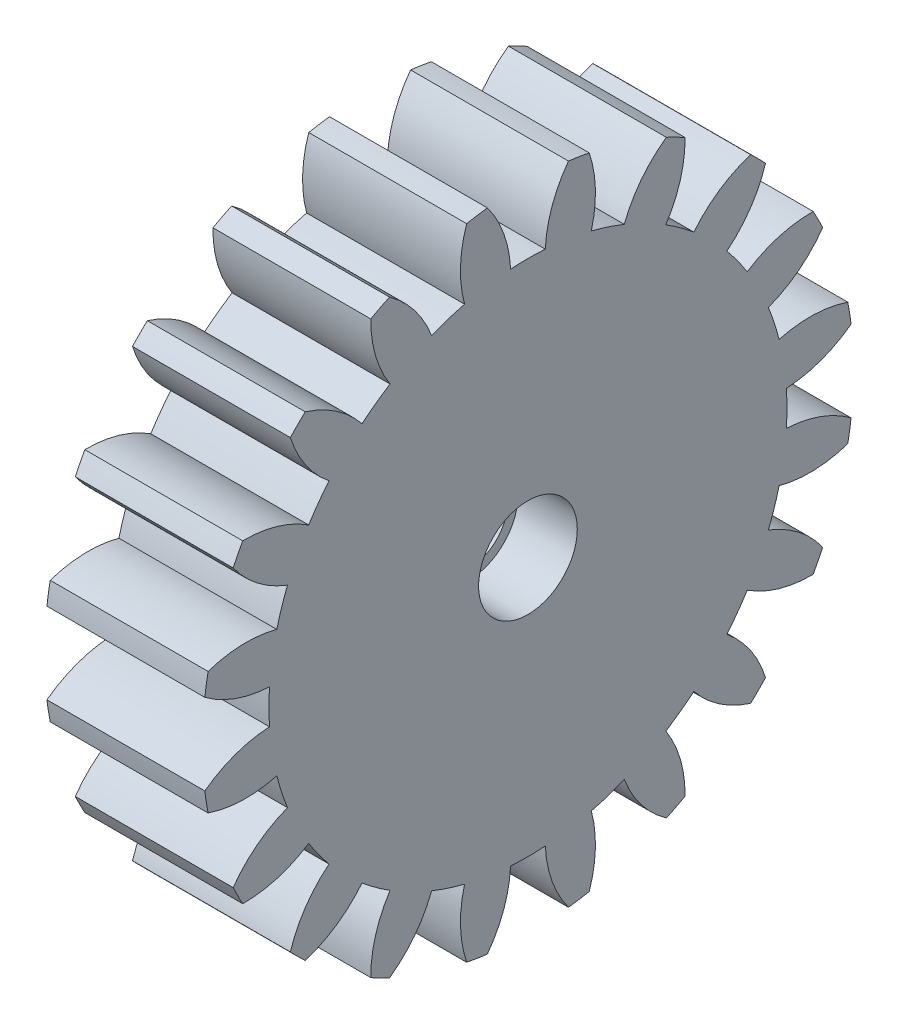
SolidWorks part; units mm, degrees
ref_plane "Plane1" through (0, 0, 0) normal (0, 0, 1) x (1, 0, 0)
ref_plane "Plane2" through (0, 0, 0) normal (0, 1, 0) x (1, 0, 0)
ref_plane "Plane3" through (0, 0, 0) normal (1, 0, 0) x (0, 0, -1)
other "Configuration Table"
sketch "HoldingSke" plane through (0, 0, 0) normal (0, 1, 0) x (1, 0, 0)
  line L0 (0, 0) -> (0.6265, -0.228)
  line L1 (-15, 0) -> (100, 0) construction
  line L2 (0, 0) -> (-2.1039, 2.3779)
  line L3 (0, 0) -> (-11.863, 4.5341)
  line L4 (0, 0) -> (8.1152, 2.9537)
  line L5 (0, 0) -> (-46.8476, -17.4728)
  line L6 (0, 0) -> (-6.6317, -4.4744)
  line L7 (-2.1039, 2.3779) -> (8.6586, 51.2059)
  line L8 (-76.2, 54.61) -> (-75.5, 54.61)
  line L9 (-67.7845, 28.3722) -> (-49.3413, 33.142)
  line L10 (-76.2, 71.12) -> (104.1128, 71.12)
  line L11 (0, 0) -> (-8, 0)
  line L12 (-76.2, 101.6) -> (-76.147, 101.6)
  line L13 (24.9733, 27.94) -> (52.9518, 28.4284)
  line L14 (24.9733, 27.94) -> (24.9743, 27.94)
  line L15 (24.9733, 27.94) -> (100.4006, 29.5858)
  line L16 (-63.627, -1.5) -> (-12.827, -1.5)
  circle A0 centre (0, 0) radius 2
  circle A1 centre (0, 0) radius 13.124
  circle A2 centre (0, 0) radius 37.5
  circle A3 centre (0, 0) radius 2
  dimension "MHD" = 26.248
  dimension "Hub_dia" = 75
  dimension "Bore" = 4
  dimension "MBD" = 4
  dimension "Num_teeth" = 20
  dimension "Pitch" = 0.6667
  dimension "Overall_len" = 50
  dimension "Show_teeth" = 20
  dimension "Thickness" = 8
  dimension "OAL" = 50.0001
  dimension "T_dim" = 0.7
  dimension "Ap" = 14.5
  dimension "H" = 19.05
  dimension "Pitch_radius" = 180.3128
  dimension "Width" = 8
  dimension "Backlash" = 0.053
  dimension "Addendum_fac" = 1
  dimension "Dedendum_fac" = 1.25
  dimension "Clearance_fac" = 0.25
  dimension "Dedendum_add" = 0.001
  dimension "Module" = 1.5
sketch "BasProSke" plane through (0, 0, 0) normal (0, 1, 0) x (1, 0, 0)
  line L0 (-10, 0) -> (60, 0) construction
  line L1 (0, 0) -> (0, 16.5)
  line L2 (0, 0) -> (8, 0)
  line L3 (8, 0) -> (8, 16.5)
  line L4 (8, 16.5) -> (0, 16.5)
  dimension "Thickness" = 8
  dimension "Diameter" = 33
revolve "Base-Revolve" add sketch "BasProSke" angle 360 about L0
sketch "TooCutSke" plane through (0, 0, 0) normal (1, 0, 0) x (0, 0, -1)
  line L1 (0, 0) -> (0, 107) construction
  line L2 (0, 0) -> (-1.2696, 14.9462) construction
  line L3 (0, 0) -> (-4.6808, 29.5532) construction
  line L4 (-1.2696, 14.9462) -> (-2.3404, 14.7766) construction
  arc A0 (0.8779, 13.0946) -> (-0.8779, 13.0946) centre (0, 0) ccw
  arc A1 (2.0711, 16.3951) -> (-2.0711, 16.3951) centre (0, 0) ccw
  circle A2 centre (0, 0) radius 15 construction
  circle A3 centre (0, 0) radius 14.5222 construction
  arc A4 (-0.8779, 13.0946) -> (-2.0711, 16.3951) centre (-6.8704, 12.7942) ccw
  arc A5 (2.0711, 16.3951) -> (0.8779, 13.0946) centre (6.8704, 12.7942) ccw
  dimension "Root_dia" = 26.248
  dimension "Overcut_dia" = 33.0508
  dimension "Pitch_dia" = 30
  dimension "Base_dia" = 29.0444
  dimension "Flank_rad" = 6
  dimension "Half_ang" = 9
  dimension "Half_CT" = 1.0841
extrude "ToothCut" cut sketch "TooCutSke" along normal through all
fillet "Breaks" [suppressed] radius 0.03
fillet "RootFillets" [suppressed] radius 0.376
pattern_circular "TeethCuts" count 20 every 18 about axis through (-10, 0, 0) along (1, 0, 0) of "ToothCut", "RootFillets", "Breaks"
sketch "HubNeaOneSke" plane through (0, 0, 0) normal (-1, 0, 0) x (0, 0, 1)
  circle A0 centre (0, 0) radius 13.124
  dimension "Diameter" = 26.248
extrude "HubNearOne" [suppressed] add sketch "HubNeaOneSke" along normal blind 42.0001
sketch "HubNeaBotSke" plane through (0, 0, 0) normal (-1, 0, 0) x (0, 0, 1)
  circle A0 centre (0, 0) radius 13.124
  dimension "Diameter" = 26.248
extrude "HubNearBoth" [suppressed] add sketch "HubNeaBotSke" along normal blind 21
ref_plane "FarPln" through (8, 0, 0) normal (1, 0, 0) x (0, 0, -1)
sketch "HubFarSke" plane through (8, 0, 0) normal (1, 0, 0) x (0, 0, -1)
  circle A0 centre (0, 0) radius 13.124
  dimension "Diameter" = 26.248
extrude "HubFar" [suppressed] add sketch "HubFarSke" along normal blind 21
sketch "BorSke" plane through (0, 0, 0) normal (1, 0, 0) x (0, 0, -1)
  circle A0 centre (0, 0) radius 2
  dimension "Diameter" = 4
extrude "Bore" cut sketch "BorSke" along normal mid plane 100.0001
sketch "KeySke" plane through (0, 0, 0) normal (1, 0, 0) x (0, 0, -1)
  line L0 (-0.8, 0) -> (-0.8, 2.7)
  line L1 (-0.8, 2.7) -> (0.8, 2.7)
  line L2 (0.8, 2.7) -> (0.8, 0)
  line L3 (0, 0) -> (0, 34) construction
  line L4 (-0.8, 0) -> (0.8, 0)
  dimension "Offset" = 2.7
  dimension "Width" = 1.6
extrude "Keyway" [suppressed] cut sketch "KeySke" along normal mid plane 100.0001
pattern_circular "Keyway2" [suppressed] count 2 every 90 about axis through (-10, 0, 0) along (1, 0, 0)
sketch "Sketch1" plane through (8, 0, 0) normal (1, 0, 0) x (0, 0, -1)
  circle A0 centre (0, 0) radius 2.5
extrude "Cut-Extrude1" cut sketch "Sketch1" against normal blind 3
equation "' \"Module@HoldingSke\" = 6.35"
equation "' \"Num_teeth@HoldingSke\" = 12"
equation "' \"Ap@HoldingSke\" =  20"
equation "' \"Ap@HoldingSke\" = 20"
equation "' \"Width@HoldingSke\" = 0.5 * 25.4"
equation "' \"Hub_dia@HoldingSke\"= 1 * 25.4"
equation "' \"Hub_dia@HoldingSke\" = 1 * 25.4"
equation "' \"Overall_len@HoldingSke\" = 1.0 * 25.4"
equation "' \"Bore@HoldingSke\" = 0.75 * 25.4"
equation "' \"T_dim@HoldingSke\" = 0.1 * 25.4"
equation "' \"Width@KeySke\" = 0.25 * 25.4"
equation "' \"Show_teeth@HoldingSke\" = 13"
equation "' \"Backlash@HoldingSke\" = 0.009 * 25.4"
equation "' \"Addendum_fac@HoldingSke\" = 1.0"
equation "' \"Dedendum_fac@HoldingSke\" = 1.25"
equation "' \"Dedendum_add@HoldingSke\" = 0.00005 * 25.4"
equation "' \"Clearance_fac@HoldingSke\" = 0.25"
equation "\"Pitch@HoldingSke\" = 1 / \"Module@HoldingSke\""
equation "\"Overcut_dia@TooCutSke\" = (\"Num_teeth@HoldingSke\" + 2 * \"Addendum_fac@HoldingSke\") / \"Pitch@HoldingSke\" + 0.002 * 25.4"
equation "\"Pitch_dia@TooCutSke\" = \"Num_teeth@HoldingSke\" / \"Pitch@HoldingSke\""
equation "\"Base_dia@TooCutSke\" = \"Num_teeth@HoldingSke\" / \"Pitch@HoldingSke\" * cos((\"Ap@HoldingSke\"  * 3.14159265 / 180))"
equation "\"Root_dia@TooCutSke\" = (\"Num_teeth@HoldingSke\" + 2) / \"Pitch@HoldingSke\" - 2 * (\"Addendum_fac@HoldingSke\" + \"Dedendum_fac@HoldingSke\") / \"Pitch@HoldingSke\" - \"Dedendum_add@HoldingSke\" * 2"
equation "\"Half_ang@TooCutSke\" = 180 / \"Num_teeth@HoldingSke\""
equation "\"Half_CT@TooCutSke\" = \"Num_teeth@HoldingSke\" / \"Pitch@HoldingSke\" * sin((3.14159265 / 2 / \"Num_teeth@HoldingSke\")) / 2 - 7 * \"Backlash@HoldingSke\" / 4"
equation "\"Flank_rad@TooCutSke\" = \"Num_teeth@HoldingSke\" / \"Pitch@HoldingSke\" / 5"
equation "\"Radius@RootFillets\" = \"Clearance_fac@HoldingSke\" / \"Pitch@HoldingSke\" + \"Dedendum_add@HoldingSke\""
equation "\"Break_rad@Breaks\" = 0.02 / \"Pitch@HoldingSke\""
equation "\"Thickness@HoldingSke\" = \"Width@HoldingSke\""
equation "\"OAL@HoldingSke\" = \"Thickness@HoldingSke\""
equation "\"MHD@HoldingSke\" = (\"Num_teeth@HoldingSke\" + 2) / \"Pitch@HoldingSke\" - 2 * (\"Addendum_fac@HoldingSke\" + \"Dedendum_fac@HoldingSke\")  / \"Pitch@HoldingSke\" - \"Dedendum_add@HoldingSke\" * 2"
equation "\"MBD@HoldingSke\" = (\"Num_teeth@HoldingSke\" + 2) / \"Pitch@HoldingSke\" - 2 * (\"Addendum_fac@HoldingSke\" + \"Dedendum_fac@HoldingSke\")  / \"Pitch@HoldingSke\" - \"Dedendum_add@HoldingSke\" * 2 - 0.002 * 25.4"
equation "\"MHD@HoldingSke\" = ((sgn( \"MHD@HoldingSke\" - \"Hub_dia@HoldingSke\" )-1)*( \"MHD@HoldingSke\" - \"Hub_dia@HoldingSke\" ))/-2+ \"Hub_dia@HoldingSke\""
equation "\"MBD@HoldingSke\" = ((sgn( \"MBD@HoldingSke\" - \"Bore@HoldingSke\" )-1)*( \"MBD@HoldingSke\" - \"Bore@HoldingSke\" ))/-2+ \"Bore@HoldingSke\""
equation "\"OAL@HoldingSke\" = ((sgn( \"OAL@HoldingSke\" - \"Overall_len@HoldingSke\" )+1)*( \"OAL@HoldingSke\" - \"Overall_len@HoldingSke\" ))/2 + \"Overall_len@HoldingSke\" + 0.000002 * 25.4"
equation "\"Num_teeth@TeethCuts\" = int( \"Show_teeth@HoldingSke\" ) + 1"
equation "\"Num_teeth@TeethCuts\" = ((sgn( \"Num_teeth@TeethCuts\" - \"Num_teeth@HoldingSke\" )-1)*( \"Num_teeth@TeethCuts\" - \"Num_teeth@HoldingSke\" ))/-2+ \"Num_teeth@HoldingSke\""
equation "\"Num_teeth@TeethCuts\" = ((sgn( \"Num_teeth@TeethCuts\" - 2.0)+1)*( \"Num_teeth@TeethCuts\" - 2.0))/2 +2.0"
equation "\"Angle@TeethCuts\" = 360.0 / \"Num_teeth@HoldingSke\""
equation "\"Diameter@BasProSke\" = (\"Num_teeth@HoldingSke\" + 2 * \"Addendum_fac@HoldingSke\") / \"Pitch@HoldingSke\""
equation "\"Thickness@BasProSke\"  = \"Thickness@HoldingSke\""
equation "' \"Fillet_rad@BasProSke\" =  \"Thickness@HoldingSke\" * 0.05"
equation "' \"Fillet_rad@BasProSke\" = \"Thickness@HoldingSke\" * 0.05"
equation "\"MHD@HoldingSke\" = ((sgn( \"MHD@HoldingSke\" - \"Root_dia@TooCutSke\" )-1)*( \"MHD@HoldingSke\" - \"Root_dia@TooCutSke\" ))/-2+ \"Root_dia@TooCutSke\""
equation "\"Diameter@HubNeaOneSke\" = \"MHD@HoldingSke\""
equation "\"Length@HubNearOne\" = \"OAL@HoldingSke\" - \"Thickness@BasProSke\""
equation "\"Diameter@HubNeaBotSke\" = \"MHD@HoldingSke\""
equation "\"Length@HubNearBoth\" = ( \"OAL@HoldingSke\" - \"Thickness@BasProSke\" ) / 2.0"
equation "\"Thickness@FarPln\" = \"Thickness@BasProSke\""
equation "\"Diameter@HubFarSke\" = \"MHD@HoldingSke\""
equation "\"Length@HubFar\" = ( \"OAL@HoldingSke\" - \"Thickness@BasProSke\" ) / 2.0"
equation "\"Diameter@BorSke\" = \"MBD@HoldingSke\""
equation "\"D1@Bore\" = \"OAL@HoldingSke\" * 2.0"
equation "\"D1@Keyway\" = \"OAL@HoldingSke\" * 2.0"
equation "\"Offset@KeySke\" = \"T_dim@HoldingSke\" + \"MBD@HoldingSke\" / 2.0"
